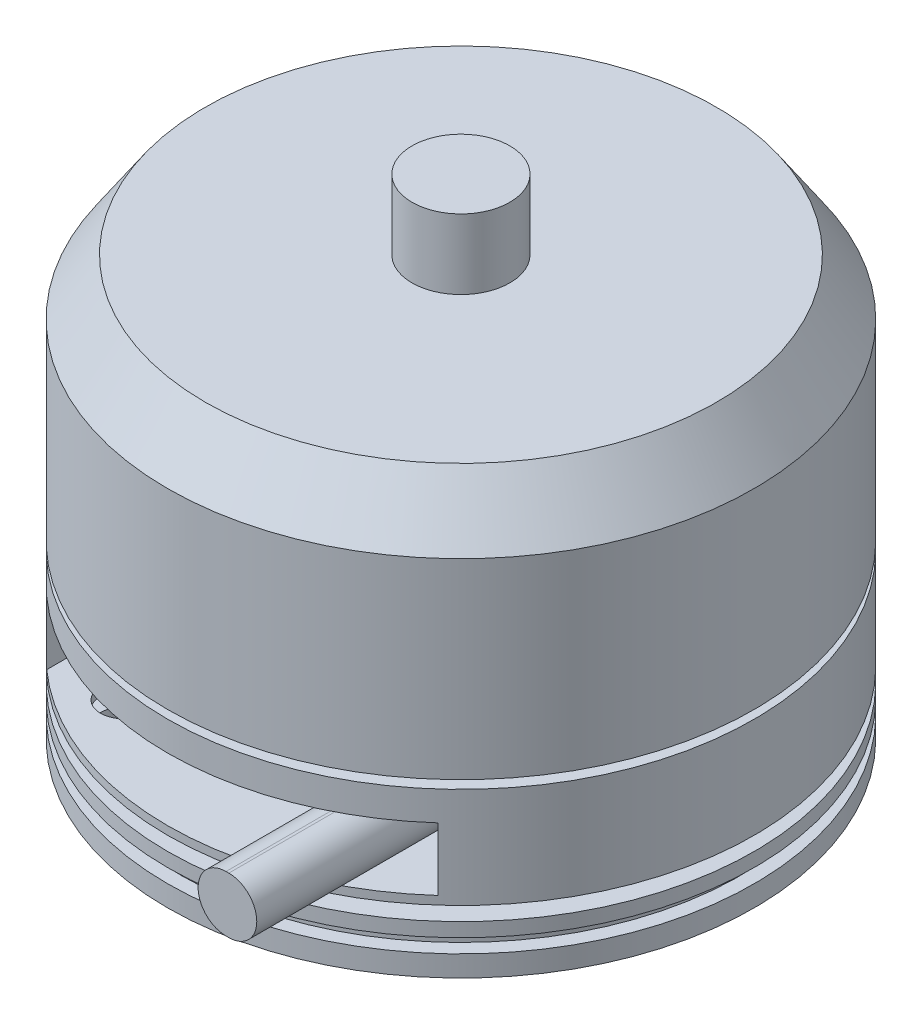
SolidWorks part; units mm, degrees
ref_plane "前视基准面" through (0, 0, 0) normal (0, 0, 1) x (1, 0, 0)
ref_plane "上视基准面" through (0, 0, 0) normal (0, 1, 0) x (1, 0, 0)
ref_plane "右视基准面" through (0, 0, 0) normal (1, 0, 0) x (0, 0, -1)
sketch "草图1" plane through (0, 0, 0) normal (0, 0, 1) x (1, 0, 0)
  line L0 (0, 0) -> (4.1, 0)
  line L1 (4.1, 0) -> (4.1, 6.7)
  line L2 (4.1, 6.7) -> (13.4, 6.7)
  line L3 (13.4, 6.7) -> (13.4, 8.7)
  line L4 (13.4, 8.7) -> (21, 8.7)
  line L5 (21, 8.7) -> (21, 10.2)
  line L6 (21, 10.2) -> (20, 10.2)
  line L7 (20, 10.2) -> (20, 11.2)
  line L8 (20, 11.2) -> (21, 11.2)
  line L9 (21, 11.2) -> (21, 12.2)
  line L10 (21, 12.2) -> (10, 12.2)
  line L11 (10, 12.2) -> (10, 13.2)
  line L12 (10, 13.2) -> (21, 13.2)
  line L13 (21, 13.2) -> (21, 20.4)
  line L14 (21, 20.4) -> (5, 20.4)
  line L15 (5, 20.4) -> (5, 21)
  line L16 (5, 21) -> (21, 21)
  line L17 (21, 21) -> (21, 34.7)
  line L18 (21, 34.7) -> (18.3, 38.7)
  line L19 (18.3, 38.7) -> (3.5, 38.7)
  line L20 (3.5, 38.7) -> (3.5, 43.7)
  line L21 (3.5, 43.7) -> (0, 43.7)
  line L22 (0, 43.7) -> (0, 0) construction
  line L23 (0, 0) -> (0, 43.7)
  dimension "D1" = 8.2
  dimension "D2" = 26.8
  dimension "D3" = 42
  dimension "D4" = 10
  dimension "D5" = 1.5
  dimension "D6" = 1
  dimension "D7" = 1
  dimension "D8" = 20
  dimension "D9" = 1
  dimension "D10" = 7.2
  dimension "D11" = 0.6
  dimension "D12" = 13.7
  dimension "D13" = 5
  dimension "D14" = 2
  dimension "D15" = 6.7
  dimension "D16" = 1
  dimension "D17" = 7
  dimension "D18" = 36.6
  dimension "D19" = 4
  dimension "D20" = 30
revolve "旋转1" add sketch "草图1" angle 360 about L22
ref_plane "基准面1" through (0, 0, 21) normal (0, 0, 1) x (1, 0, 0)
sketch "草图2" plane through (0, 0, 21) normal (0, 0, 1) x (1, 0, 0)
  line L1 (-14, 18.3) -> (14, 18.3)
  line L2 (-14, 18.3) -> (-14, 13.8)
  line L3 (-14, 13.8) -> (14, 13.8)
  line L4 (14, 18.3) -> (14, 13.8)
  line L5 (-14, 18.3) -> (14, 13.8) construction
  line L6 (-14, 13.8) -> (14, 18.3) construction
  line L7 (-21, 13.2) -> (21, 13.2) construction
  point P0 (0, 16.05)
  dimension "D1" = 28
  dimension "D2" = 4.5
  dimension "D3" = 0.6
extrude "切除-拉伸1" cut sketch "草图2" against normal blind 10
sketch "草图3" plane through (0, 0, 11) normal (0, 0, 1) x (1, 0, 0)
  line L0 (9.1851, 16.0532) -> (9.3851, 16.0532) construction
  line L1 (9.1851, 18.0532) -> (9.3851, 18.0532)
  line L2 (9.1851, 14.0532) -> (9.3851, 14.0532)
  arc A0 (9.1851, 18.0532) -> (9.1851, 14.0532) centre (9.1851, 16.0532) ccw
  arc A1 (9.3851, 14.0532) -> (9.3851, 18.0532) centre (9.3851, 16.0532) ccw
  point P2 (9.2851, 16.0532)
  dimension "D1" = 4
  dimension "D2" = 0.2
extrude "凸台-拉伸1" add sketch "草图3" along normal blind 15
sketch "草图7" plane through (0, 8.7, 0) normal (0, -1, 0) x (1, 0, 0)
  line L0 (-9.3687, 14.781) -> (9.3687, -14.781) construction
  line L1 (14.781, 9.3687) -> (-14.781, -9.3687) construction
  circle A0 centre (-9.3687, 14.781) radius 1.5
  circle A1 centre (-14.781, -9.3687) radius 1.5
  circle A2 centre (14.781, 9.3687) radius 1.5
  circle A3 centre (9.3687, -14.781) radius 1.5
  circle A4 centre (0, 0) radius 17.5 construction
  dimension "D2" = 35
  dimension "D1" = 3
hole_wizard "M4 螺纹孔2" positions "3D草图2" profile "草图10" tap size "M4" standard "GB"
sketch3d "3D草图2"
  point P0 (-14.781, 8.7, -9.3687)
  point P3 (-9.3687, 8.7, 14.781)
  point P6 (9.3687, 8.7, -14.781)
  point P9 (14.781, 8.7, 9.3687)
sketch "草图10" plane through (-14.781, 8.7, -9.3687) normal (1, 0, 0) x (0, 0, -1)
  line L0 (0, 0) -> (0, 11.4914)
  line L1 (0, 11.4914) -> (1.65, 10.5)
  line L2 (1.65, 10.5) -> (1.65, 0)
  line L5 (1.65, 0) -> (0, 0)
  line L10 (0, 11.4914) -> (-1.65, 10.5) construction
  line L11 (0, -6.35) -> (0, 107.95) construction
  dimension "螺纹孔钻头直径" = 3.3
  dimension "螺纹孔钻头深度" = 10.5
  dimension "导头角度" = 118
cosmetic thread "孔螺蚊线6" parameters "D1"=8, "D2"=4
cosmetic thread "孔螺蚊线7" parameters "D1"=8, "D2"=4
cosmetic thread "孔螺蚊线8" parameters "D1"=8, "D2"=4
cosmetic thread "孔螺蚊线9" parameters "D1"=8, "D2"=4
